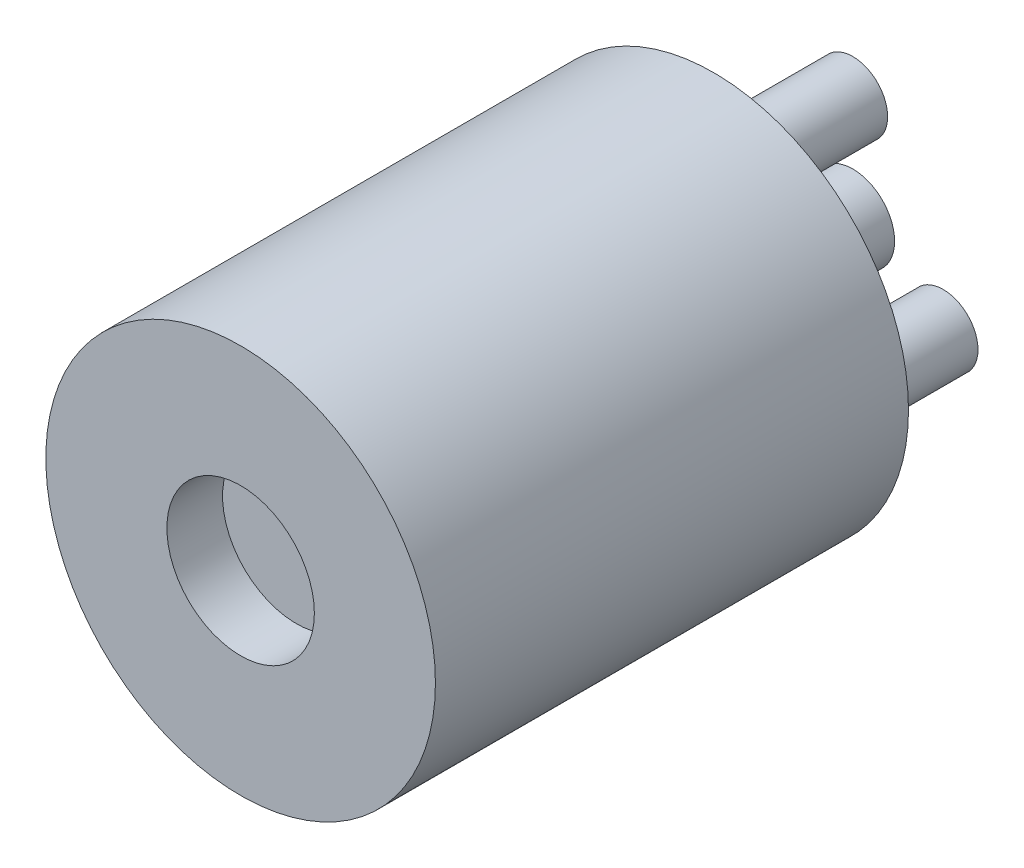
SolidWorks part; units mm, degrees
ref_plane "Front Plane" through (0, 0, 0) normal (0, 0, 1) x (1, 0, 0)
ref_plane "Top Plane" through (0, 0, 0) normal (0, 1, 0) x (1, 0, 0)
ref_plane "Right Plane" through (0, 0, 0) normal (1, 0, 0) x (0, 0, -1)
sketch "Sketch1" plane through (0, 0, 0) normal (0, 0, 1) x (1, 0, 0)
  circle A2 centre (-43.4831, -66.2391) radius 1.25
  circle A3 centre (-43.4831, -66.2391) radius 1.25
  circle A5 centre (-40.2355, -71.8641) radius 1.25
  circle A6 centre (-40.2355, -71.8641) radius 1.25
  circle A8 centre (-46.7307, -71.8641) radius 1.25
  circle A9 centre (-46.7307, -71.8641) radius 1.25
  circle A11 centre (-43.4831, -69.9891) radius 7
  circle A12 centre (-43.4831, -69.9891) radius 7
  dimension "D1" = 0
  dimension "D2" = 0
  dimension "D3" = 0
  dimension "D4" = 1
extrude "Boss-Extrude1" add sketch "Sketch1" along normal blind 17
sketch "Sketch2" plane through (0, 0, 17) normal (0, 0, 1) x (1, 0, 0)
  circle A2 centre (-43.4831, -69.9891) radius 7
  circle A3 centre (-43.4831, -69.9891) radius 7
  dimension "D1" = 0
extrude "Boss-Extrude2" add sketch "Sketch2" against normal blind 11
sketch "Sketch3" plane through (0, 0, 17) normal (0, 0, 1) x (1, 0, 0)
  circle A1 centre (-43.4831, -69.9891) radius 2.65
  circle A2 centre (-43.4831, -69.9891) radius 7
  circle A3 centre (-43.4831, -69.9891) radius 7
  dimension "D2" = 5.3
  dimension "D1" = 0
extrude "Cut-Extrude1" cut sketch "Sketch3" against normal blind 2 contours A1
sketch "Sketch4" plane through (0, 0, 0) normal (0, 0, -1) x (-1, 0, 0)
  circle A0 centre (43.4831, -69.9891) radius 1.5
  circle A1 centre (43.4831, -69.9891) radius 7 construction
  dimension "D1" = 0
  dimension "D2" = 3
extrude "Boss-Extrude3" add sketch "Sketch4" along normal blind 5
sketch "Sketch5" plane through (0, 0, 0) normal (0, 0, -1) x (-1, 0, 0)
  circle A2 centre (43.4831, -66.2391) radius 1.25
  circle A3 centre (43.4831, -66.2391) radius 1.25
  circle A5 centre (46.7307, -71.8641) radius 1.25
  circle A6 centre (46.7307, -71.8641) radius 1.25
  circle A8 centre (40.2355, -71.8641) radius 1.25
  circle A9 centre (40.2355, -71.8641) radius 1.25
  dimension "D1" = 0
  dimension "D2" = 0
  dimension "D3" = 0
extrude "Boss-Extrude4" add sketch "Sketch5" along normal mid plane 10
sketch "Sketch6" plane through (0, 0, 0) normal (0, 0, -1) x (-1, 0, 0)
  circle A2 centre (43.4831, -69.9891) radius 7
  circle A3 centre (43.4831, -69.9891) radius 7
  dimension "D1" = 0
extrude "Boss-Extrude5" add sketch "Sketch6" against normal up to surface (15 mm away) up to face at (-40.8331, -69.9891, 15)
